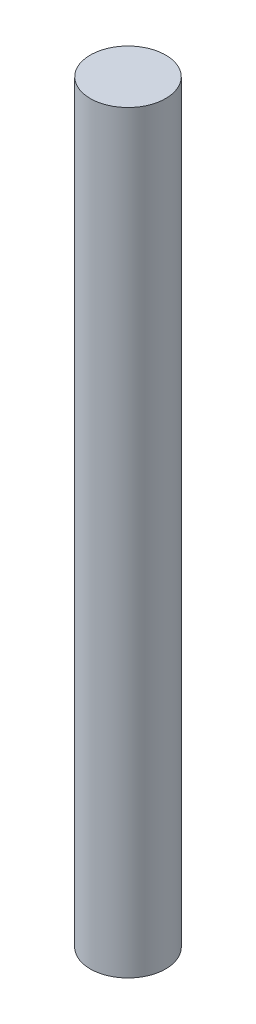
SolidWorks part; units mm, degrees
ref_plane "Front Plane" through (0, 0, 0) normal (0, 0, 1) x (1, 0, 0)
ref_plane "Top Plane" through (0, 0, 0) normal (0, 1, 0) x (1, 0, 0)
ref_plane "Right Plane" through (0, 0, 0) normal (1, 0, 0) x (0, 0, -1)
sketch "Sketch1" plane through (0, 0, 0) normal (0, 1, 0) x (1, 0, 0)
  circle A0 centre (0, 0) radius 10
  dimension "D1" = 20
extrude "Boss-Extrude1" add sketch "Sketch1" along normal mid plane 200
